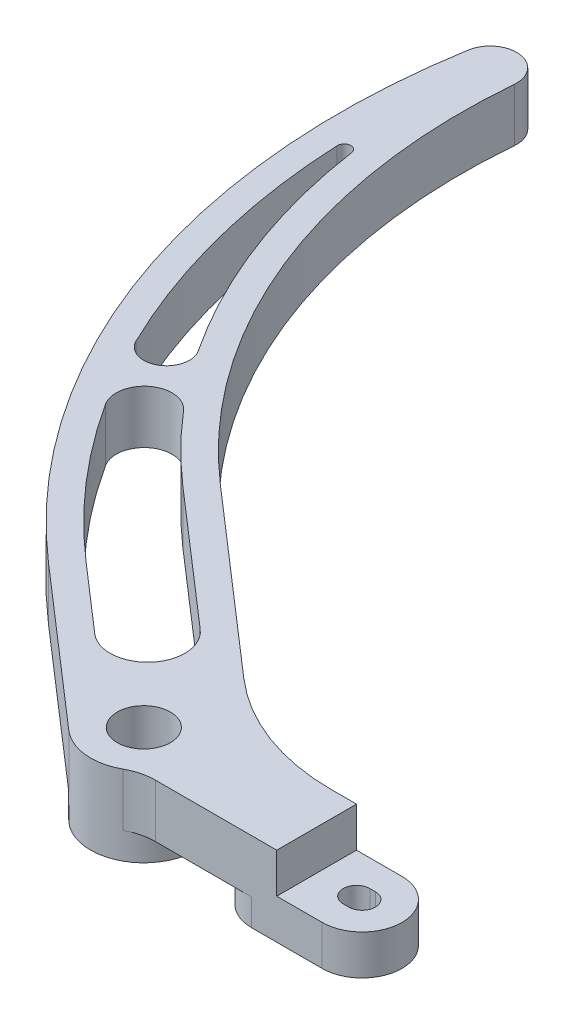
SolidWorks part; units mm, degrees
material "6061-T6 (SS)"
ref_plane "Front Plane" through (0, 0, 0) normal (0, 0, 1) x (1, 0, 0)
ref_plane "Top Plane" through (0, 0, 0) normal (0, 1, 0) x (1, 0, 0)
ref_plane "Right Plane" through (0, 0, 0) normal (1, 0, 0) x (0, 0, -1)
sketch "Sketch1" plane through (0, 0, 0) normal (0, 1, 0) x (1, 0, 0)
  line L0 (0, 0) -> (0, -165.1) construction
  line L1 (0, -165.1) -> (1.3399, -165.1) construction
  line L2 (0, -161.925) -> (1.3399, -161.925)
  line L3 (0, -168.275) -> (1.3399, -168.275)
  line L4 (1.3399, -174.625) -> (-42.3997, -174.625)
  line L5 (1.3399, -155.575) -> (-15.557, -155.575)
  line L6 (-91.9014, -105.7205) -> (-48.8848, -143.1142)
  line L7 (-59.1319, -174.6848) -> (-96.2538, -142.4153)
  line L8 (-50.8, -165.1) -> (0, -153.1955) construction
  line L9 (-139.5532, 12.1493) -> (-50.8, -165.1) construction
  line L10 (0, -165.1) -> (-50.8, -165.1) construction
  line L11 (-50.8, -165.1) -> (-177.6532, -12.7757) construction
  line L12 (-1.3399, -153.5095) -> (0, -153.5095) construction
  circle A0 centre (0, 0) radius 140.081 construction
  circle A1 centre (-50.8, -165.1) radius 6.35
  arc A2 (-139.5532, 12.1493) -> (-91.9014, -105.7205) centre (0, 0) ccw
  arc A3 (0, -161.925) -> (0, -168.275) centre (0, -165.1) ccw
  arc A4 (1.3399, -168.275) -> (1.3399, -161.925) centre (1.3399, -165.1) ccw
  arc A5 (1.3399, -155.575) -> (1.3399, -174.625) centre (1.3399, -165.1) cw
  arc A6 (-42.3997, -174.625) -> (-59.1319, -174.6848) centre (-50.8, -165.1) cw
  arc A7 (-15.557, -155.575) -> (-48.8848, -143.1142) centre (-15.557, -104.775) cw
  arc A8 (-96.2538, -142.4153) -> (-152.1399, 13.7613) centre (14.8935, -14.555) cw
  arc A9 (-152.1399, 13.7613) -> (-139.5532, 12.1493) centre (-145.8792, 12.7) cw
  circle A10 centre (-50.8, -165.1) radius 50.8 construction
  arc A11 (-67.0543, -145.5819) -> (-62.1724, -142.3881) centre (-50.8, -165.1) cw construction
  arc A12 (-25.4, -165.1) -> (-26.07, -159.3048) centre (-50.8, -165.1) ccw construction
  circle A13 centre (-1.3399, -153.5095) radius 9.525 construction
  point P0 (0.67, -165.1)
  dimension "D1" = 280.162
  dimension "D2" = 50.8
  dimension "D4" = 3.175
  dimension "D5" = 9.525
  dimension "D6" = 6.35
  dimension "D7" = 12.7
  dimension "D9" = 6.35
  dimension "D11" = 25.4
  dimension "D3" = 101.6
  dimension "D8" = 49
  dimension "D10" = 38.1
  dimension "D12" = 165.1
  dimension "D13" = 12.7
extrude "Boss-Extrude1" add sketch "Sketch1" along normal blind 12.7
sketch "Sketch3" plane through (0, 12.7, 0) normal (0, 1, 0) x (1, 0, 0)
  line L0 (-126.7212, -83.7361) -> (-116.6134, -99.2045) construction
  line L1 (-50.8, -165.1) -> (-70.134, -144.8817) construction
  line L2 (-53.0508, -147.9067) -> (-96.0674, -110.5129)
  line L3 (-64.2789, -138.1462) -> (-96.0674, -110.5129)
  line L4 (-146.4309, -21.6211) -> (-126.7212, -83.7361) construction
  line L5 (-92.0878, -137.6229) -> (-54.966, -169.8924)
  line L6 (-92.0878, -137.6229) -> (-75.9891, -151.6173)
  line L7 (-116.6134, -99.2045) -> (-70.134, -144.8817) construction
  arc A0 (-122.1683, -80.7276) -> (-131.6245, -86.1314) centre (-126.7212, -83.7361) cw
  arc A1 (-122.2227, -102.8151) -> (-111.5323, -94.8819) centre (-116.6134, -99.2045) cw
  arc A2 (-122.2227, -102.8151) -> (-92.0878, -137.6229) centre (14.8935, -14.555) ccw
  arc A3 (-148.0169, -21.6906) -> (-144.8604, -21.3892) centre (-146.4309, -21.6211) cw
  arc A4 (-111.5323, -94.8819) -> (-96.0674, -110.5129) centre (0, 0) ccw
  arc A5 (-145.8792, 12.7) -> (-92.0878, -137.6229) centre (14.8935, -14.555) ccw
  arc A6 (-145.8792, 12.7) -> (-96.0674, -110.5129) centre (0, 0) ccw
  arc A7 (-144.8604, -21.3892) -> (-122.1683, -80.7276) centre (0, 0) ccw
  arc A8 (-148.0169, -21.6906) -> (-131.6245, -86.1314) centre (14.8935, -14.555) ccw
  arc A9 (-64.2789, -138.1462) -> (-75.9891, -151.6173) centre (-70.134, -144.8817) cw
  circle A10 centre (-50.8, -165.1) radius 6.35 construction
  point P16 (-123.7361, -88.3043)
  point P17 (-120.2625, -93.6201)
  point P21 (-63.9659, -151.3319)
  point P22 (-55.1886, -160.5106)
  dimension "D3" = 1.5875
  dimension "D4" = 6.35
  dimension "D5" = 12.7
  dimension "D1" = 6.35
  dimension "D2" = 6.35
extrude "Cut-Extrude2" cut sketch "Sketch3" against normal through all
fillet "Fillet1" radius 12.7 1 edges at (-42.3997, 6.35, 174.625)
sketch "Sketch4" plane through (0, 0, 0) normal (0, 1, 0) x (1, 0, 0)
  line L0 (1.3399, -165.1) -> (-15.557, -165.1) construction
  line L1 (1.3399, -174.625) -> (-15.557, -174.625)
  line L2 (1.3399, -155.575) -> (-15.557, -155.575)
  line L3 (1.3399, -161.925) -> (0, -161.925) construction
  line L4 (0, -168.275) -> (1.3399, -168.275) construction
  line L5 (1.3399, -161.925) -> (0, -161.925)
  line L6 (0, -168.275) -> (1.3399, -168.275)
  circle A0 centre (-50.8, -165.1) radius 12.7
  circle A1 centre (-50.8, -165.1) radius 6.35 construction
  circle A2 centre (-50.8, -165.1) radius 6.35
  arc A3 (1.3399, -174.625) -> (1.3399, -155.575) centre (1.3399, -165.1) ccw
  arc A4 (-15.557, -155.575) -> (-15.557, -174.625) centre (-15.557, -165.1) ccw
  arc A5 (1.3399, -174.625) -> (1.3399, -155.575) centre (1.3399, -165.1) ccw construction
  arc A6 (0, -161.925) -> (0, -168.275) centre (0, -165.1) ccw construction
  arc A7 (1.3399, -168.275) -> (1.3399, -161.925) centre (1.3399, -165.1) ccw construction
  arc A8 (0, -161.925) -> (0, -168.275) centre (0, -165.1) ccw
  arc A9 (1.3399, -168.275) -> (1.3399, -161.925) centre (1.3399, -165.1) ccw
  point P8 (-7.1085, -165.1)
  point P16 (0, 0)
extrude "Boss-Extrude2" add sketch "Sketch4" against normal blind 6.35
sketch "Sketch2" plane through (0, 12.7, 0) normal (0, 1, 0) x (1, 0, 0)
  line L0 (1.3399, -155.575) -> (-15.557, -155.575) construction
  line L3 (-9.525, -150.4585) -> (17.5489, -150.4585)
  line L4 (-9.525, -150.4585) -> (-9.525, -180.0553)
  line L5 (-9.525, -180.0553) -> (17.5489, -180.0553)
  line L6 (17.5489, -150.4585) -> (17.5489, -180.0553)
  circle A0 centre (0, -165.1) radius 9.525 construction
extrude "Cut-Extrude1" cut sketch "Sketch2" against normal blind 9.525
